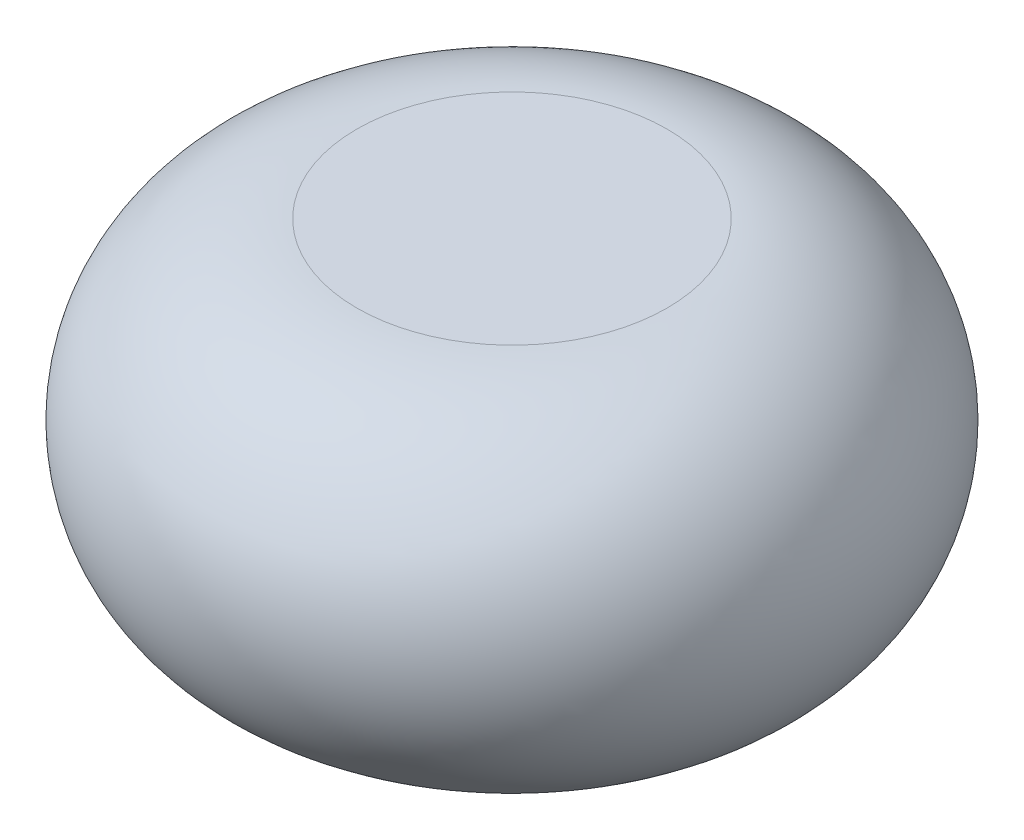
SolidWorks part; units mm, degrees
ref_plane "Front Plane" through (0, 0, 0) normal (0, 0, 1) x (1, 0, 0)
ref_plane "Top Plane" through (0, 0, 0) normal (0, 1, 0) x (1, 0, 0)
ref_plane "Right Plane" through (0, 0, 0) normal (1, 0, 0) x (0, 0, -1)
sketch "Sketch1" plane through (0, 0, 0) normal (0, 0, 1) x (1, 0, 0)
  line L0 (0, 625) -> (0, -500)
  line L1 (0, -500) -> (500, -500)
  line L3 (0, 625) -> (500, 625)
  arc A0 (500, -500) -> (500, 625) centre (500, 62.5) ccw
  point P0 (0, 0)
  dimension "D1" = 500
  dimension "D2" = 1125
  dimension "D3" = 500
ref_axis "Axis1" through (0, 550, 0) along (0, -1, 0)
revolve "Revolve2" add sketch "Sketch1" angle 360 about axis through (0, 550, 0) along (0, -1, 0)
